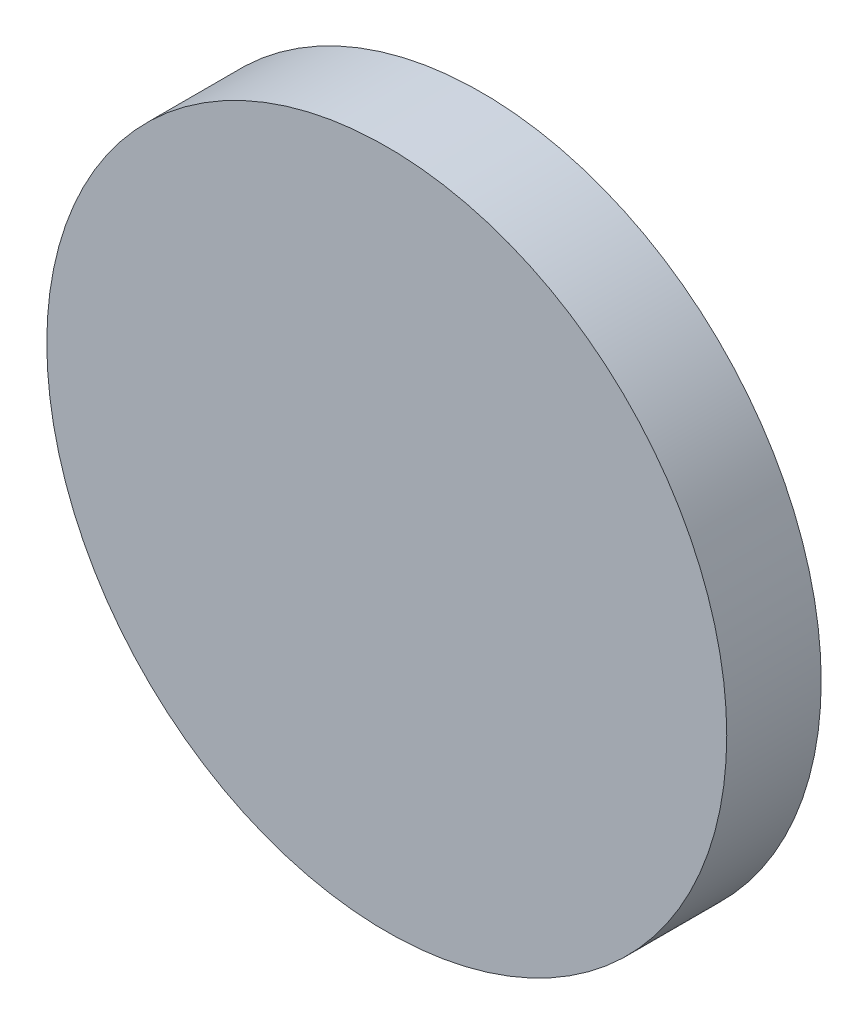
SolidWorks part; units mm, degrees
ref_plane "Plan de face" through (0, 0, 0) normal (0, 0, 1) x (1, 0, 0)
ref_plane "Plan de dessus" through (0, 0, 0) normal (0, 1, 0) x (1, 0, 0)
ref_plane "Plan de droite" through (0, 0, 0) normal (1, 0, 0) x (0, 0, -1)
sketch "Esquisse1" plane through (0, 0, 0) normal (0, 0, 1) x (1, 0, 0)
  circle A0 centre (0, 0) radius 36
  dimension "D1" = 72
extrude "Boss.-Extru.1" add sketch "Esquisse1" along normal blind 10
